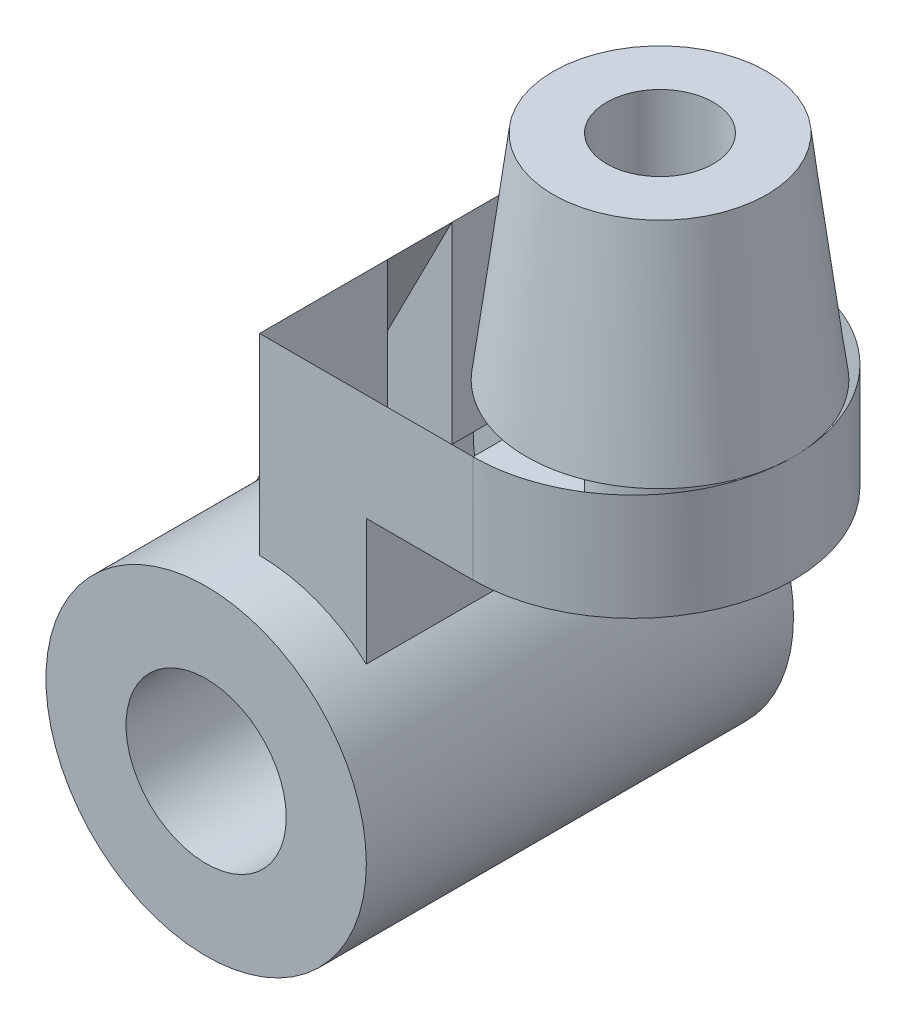
SolidWorks part; units mm, degrees
ref_plane "Front Plane" through (0, 0, 0) normal (0, 0, 1) x (1, 0, 0)
ref_plane "Top Plane" through (0, 0, 0) normal (0, 1, 0) x (1, 0, 0)
ref_plane "Right Plane" through (0, 0, 0) normal (1, 0, 0) x (0, 0, -1)
sketch "Sketch1" plane through (0, 0, 0) normal (0, 0, 1) x (1, 0, 0)
  line L0 (-65.395, 0) -> (77.7919, 0) construction
  line L1 (0, -54.402) -> (0, 81.9989) construction
  circle A0 centre (0, 0) radius 30
  circle A1 centre (0, 0) radius 15
  dimension "D1" = 30
  dimension "D2" = 60
extrude "Boss-Extrude3" add sketch "Sketch1" along normal mid plane 80
sketch "Sketch4" plane through (0, 0, 0) normal (0, 0, 1) x (1, 0, 0)
  line L0 (0, 30) -> (0, 66)
  line L1 (0, 66) -> (40, 66)
  line L2 (40, 66) -> (40, 46)
  line L3 (40, 46) -> (20, 46)
  line L4 (20, 46) -> (20, 22.3607)
  arc A0 (0, 30) -> (20, 22.3607) centre (0, 0) cw
  circle A1 centre (0, 0) radius 30 construction
  dimension "D1" = 40
  dimension "D2" = 20
  dimension "D3" = 20
  dimension "D4" = 36
  dimension "D5" = 20
extrude "Boss-Extrude4" add sketch "Sketch4" along normal mid plane 60
sketch "Sketch5" plane through (0, 66, 0) normal (0, 1, 0) x (1, 0, 0)
  line L0 (40, 30) -> (40, -30)
  arc A0 (40, 30) -> (40, -30) centre (40, 0) cw
extrude "Boss-Extrude5" add sketch "Sketch5" against normal blind 20
sketch "Sketch9" plane through (0, 0, 0) normal (0, 0, 1) x (1, 0, 0)
  line L0 (0, 66) -> (-26.7217, 13.6364)
  line L1 (0, 66) -> (0, 30)
  circle A0 centre (0, 0) radius 30 construction
  arc A1 (0, 30) -> (-26.7217, 13.6364) centre (0, 0) ccw
extrude "Boss-Extrude6" add sketch "Sketch9" along normal mid plane 12
sketch "Sketch10" plane through (0, 0, 0) normal (0, 0, 1) x (1, 0, 0)
  line L0 (20, 66) -> (45, 66)
  line L1 (40, 66) -> (0, 66) construction
  line L4 (45, 66) -> (45, 123.7603) construction
  line L5 (20, 66) -> (25, 106)
  line L6 (25, 106) -> (45, 106)
  line L7 (45, 106) -> (45, 66)
  dimension "D1" = 40
  dimension "D2" = 25
  dimension "D3" = 20
revolve "Revolve1" add sketch "Sketch10" angle 360 about L4
sketch "Sketch11" plane through (0, 106, 0) normal (0, 1, 0) x (1, 0, 0)
  circle A0 centre (45, 0) radius 10
  dimension "D1" = 20
extrude "Cut-Extrude1" cut sketch "Sketch11" against normal blind 60
